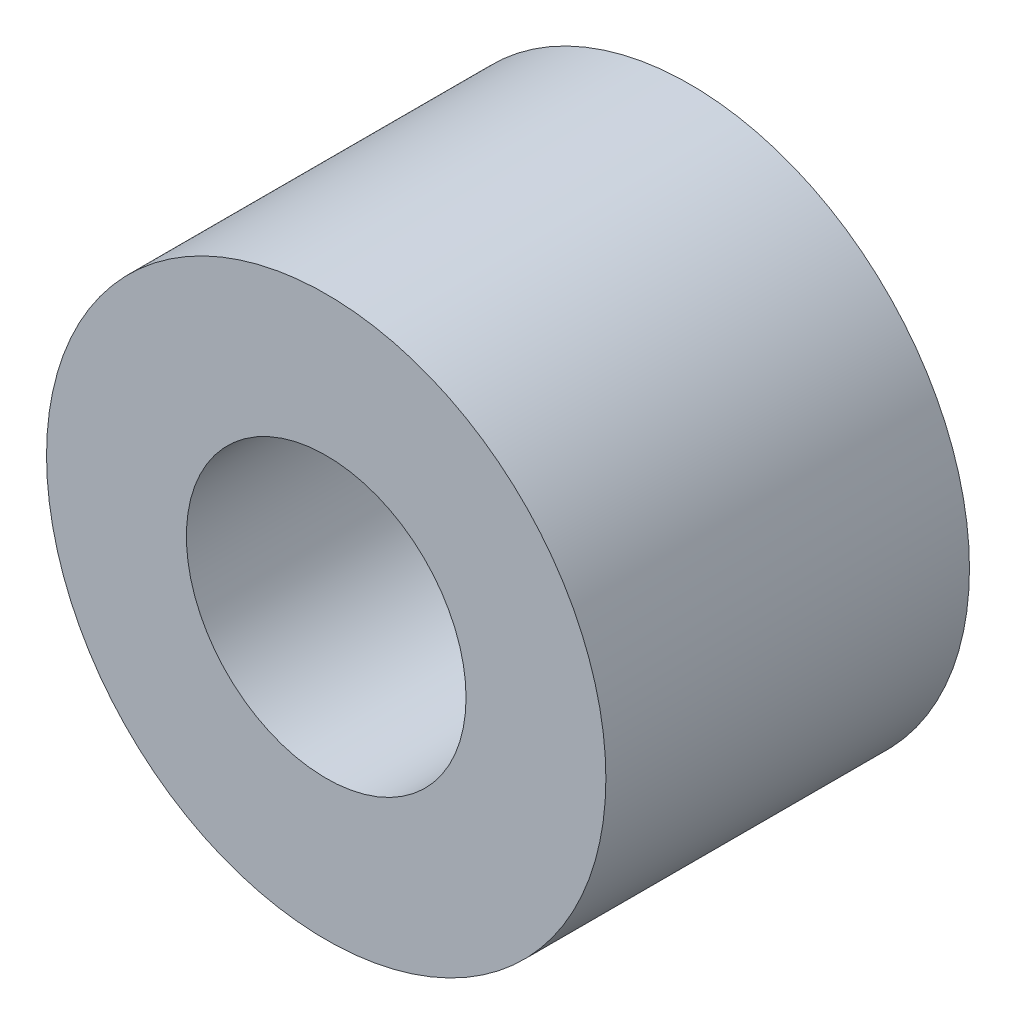
SolidWorks part; units mm, degrees
ref_plane "Front Plane" through (0, 0, 0) normal (0, 0, 1) x (1, 0, 0)
ref_plane "Top Plane" through (0, 0, 0) normal (0, 1, 0) x (1, 0, 0)
ref_plane "Right Plane" through (0, 0, 0) normal (1, 0, 0) x (0, 0, -1)
sketch "Sketch1" plane through (0, 0, 0) normal (0, 0, 1) x (1, 0, 0)
  circle A0 centre (0, 0) radius 5
  circle A1 centre (0, 0) radius 2.5
  dimension "D1" = 10
  dimension "D2" = 5
extrude "Boss-Extrude1" add sketch "Sketch1" along normal blind 6.5
